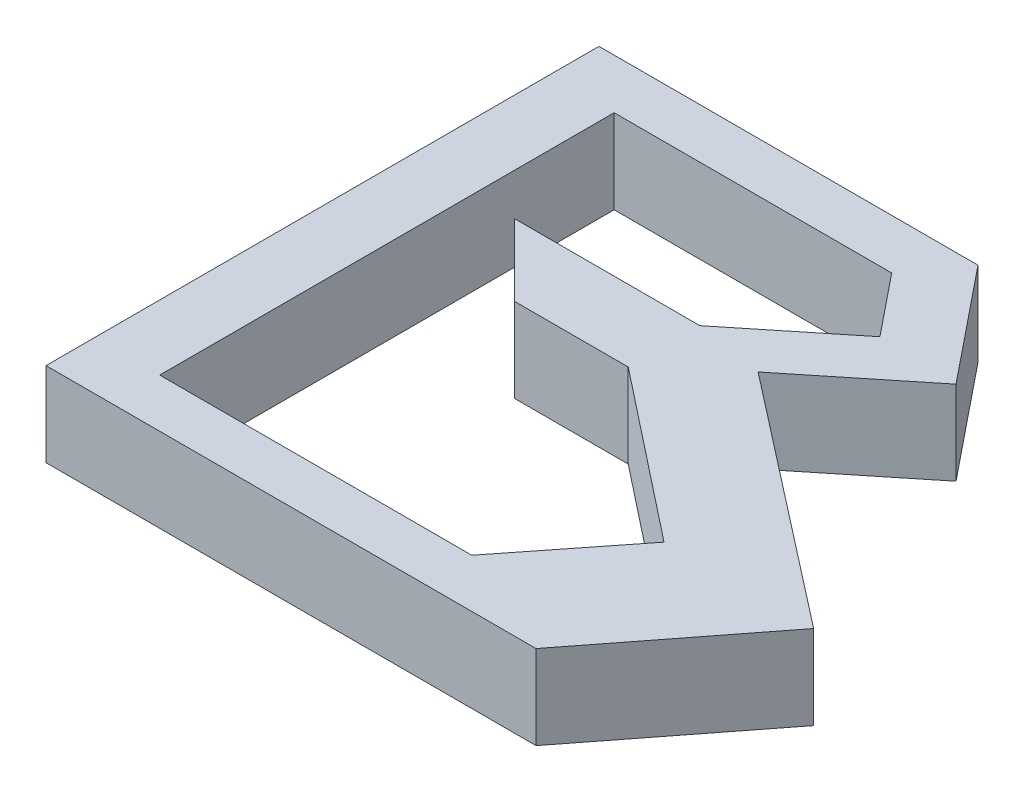
SolidWorks part; units mm, degrees
ref_plane "Front Plane" through (0, 0, 0) normal (0, 0, 1) x (1, 0, 0)
ref_plane "Top Plane" through (0, 0, 0) normal (0, 1, 0) x (1, 0, 0)
ref_plane "Right Plane" through (0, 0, 0) normal (1, 0, 0) x (0, 0, -1)
sketch "Sketch1" plane through (0, 0, 0) normal (0, 1, 0) x (1, 0, 0)
  line L0 (-31.5914, 41.6491) -> (-31.5914, -24.1126)
  line L1 (-31.5914, -24.1126) -> (26.6915, -24.1126)
  line L2 (26.6915, -24.1126) -> (41.1333, -5.5446)
  line L3 (41.1333, -5.5446) -> (11.4066, 17.5761)
  line L4 (11.4066, 17.5761) -> (24.4311, 28.0888)
  line L5 (24.4311, 28.0888) -> (13.4859, 41.6491)
  line L6 (13.4859, 41.6491) -> (-31.5914, 41.6491)
  line L7 (-23.8547, 35.7176) -> (9.1551, 35.7176)
  line L8 (9.1551, 35.7176) -> (15.0229, 28.4478)
  line L9 (15.0229, 28.4478) -> (3.1728, 18.8831)
  line L10 (3.1728, 18.8831) -> (-18.8831, 18.8831)
  line L11 (-18.8831, 18.8831) -> (-10.3652, 10.3652)
  line L12 (-10.3652, 10.3652) -> (3.1728, 10.3652)
  line L13 (3.1728, 10.3652) -> (23.3389, -5.5446)
  line L14 (23.3389, -5.5446) -> (13.2559, -18.3252)
  line L15 (13.2559, -18.3252) -> (-23.8547, -18.3252)
  line L16 (-23.8547, -18.3252) -> (-23.8547, 35.7176)
extrude "Boss-Extrude1" add sketch "Sketch1" along normal blind 10
